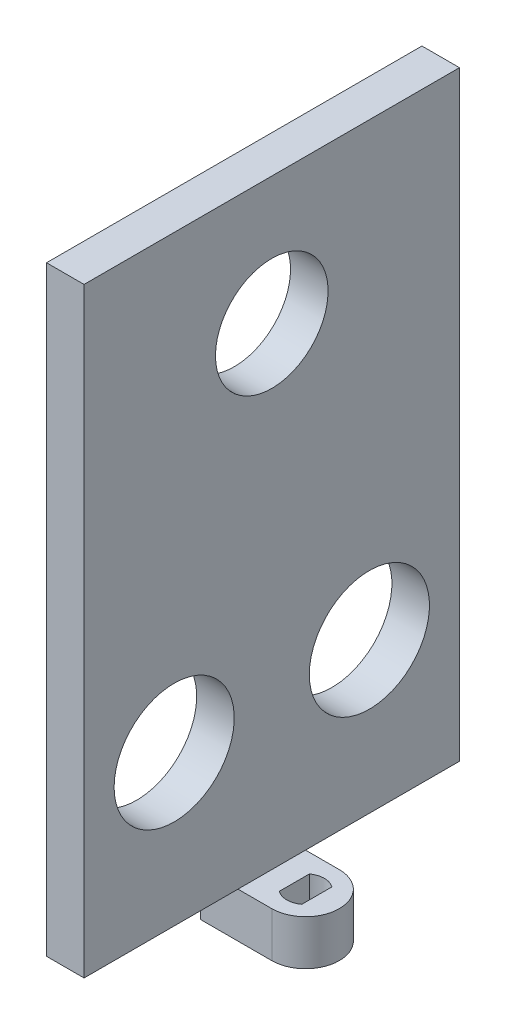
SolidWorks part; units mm, degrees
ref_plane "Alzado" through (0, 0, 0) normal (0, 0, 1) x (1, 0, 0)
ref_plane "Planta" through (0, 0, 0) normal (0, 1, 0) x (1, 0, 0)
ref_plane "Vista lateral" through (0, 0, 0) normal (1, 0, 0) x (0, 0, -1)
sketch "Croquis1" plane through (0, 0, 0) normal (0, 1, 0) x (1, 0, 0)
  line L0 (-9.5, 0) -> (-4.5, 0)
  line L1 (0, 4.5) -> (-9.5, 4.5)
  line L2 (0, 4.5) -> (0, -4.5)
  line L3 (0, -4.5) -> (-9.5, -4.5)
  line L4 (-9.5, 4.5) -> (-9.5, -4.5)
  line L5 (-1.5, -3.4467) -> (1.5, -3.4467)
  line L6 (-1.5, -3.4467) -> (-1.5, 3.4467)
  line L7 (-1.5, 3.4467) -> (1.5, 3.4467)
  line L8 (1.5, -3.4467) -> (1.5, 3.4467)
  line L9 (-1.5, -3.4467) -> (1.5, 3.4467) construction
  line L10 (-1.5, 3.4467) -> (1.5, -3.4467) construction
  line L11 (-4.5, 0) -> (4.5, 0)
  circle A0 centre (0, 0) radius 4.5
  circle A1 centre (0, 0) radius 2.5
  dimension "D1" = 9
  dimension "D2" = 5
  dimension "D3" = 3
  dimension "D4" = 5
extrude "Saliente-Extruir1" add sketch "Croquis1" along normal blind 6 contours A0 L1 L4 L0 | A0 L0 L4 L3 | A1 L6 L7 L2 A0 L11 | A1 L11 A0 L2 L5 L6 | L11 A1 L6 | L6 A1 L11 | A1 L2 L7 L6 | A1 L8 L7 L2 | A1 L6 L5 L2 | A1 L2 L5 L8 | L8 A1 L11 | L11 A1 L8 | A1 L11 A0 L2 L7 L8 | A1 L8 L5 L2 A0 L11
sketch "Croquis4" plane through (0, 6, 0) normal (0, 1, 0) x (1, 0, 0)
  line L0 (0, -4.5) -> (-9.5, -4.5) construction
  line L1 (-9.5, -25) -> (-4.5, -25)
  line L2 (-9.5, -25) -> (-9.5, 25)
  line L3 (-9.5, 25) -> (-4.5, 25)
  line L4 (-4.5, -25) -> (-4.5, 25)
  dimension "D1" = 50
  dimension "D2" = 20.5
  dimension "D3" = 5
extrude "Saliente-Extruir4" add sketch "Croquis4" along normal blind 80
sketch "Croquis5" plane through (-9.5, 0, 0) normal (-1, 0, 0) x (0, 0, 1)
  line L0 (-25, 86) -> (-25, 6) construction
  line L1 (-25, 36) -> (25, 36)
  line L2 (-25, 36) -> (-25, 16)
  line L3 (-25, 16) -> (25, 16)
  line L4 (25, 36) -> (25, 16)
  line L5 (25, 86) -> (25, 6) construction
  line L6 (-13, 26) -> (13, 26)
  line L7 (-13, 26) -> (-25, 26)
  line L8 (0, 26) -> (0, 6)
  line L9 (4.5, 6) -> (-4.5, 6) construction
  line L10 (-25, 6) -> (-4.5, 6) construction
  line L11 (25, 26) -> (-25.8331, 26)
  line L12 (0, 76.5) -> (0, 81)
  line L13 (17.5, 81) -> (-17.5, 81)
  line L14 (17.5, 81) -> (17.5, 46)
  line L15 (17.5, 46) -> (-17.5, 46)
  line L16 (-17.5, 81) -> (-17.5, 46)
  line L18 (0, 36) -> (0, 46)
  circle A0 centre (-13, 26) radius 8
  circle A1 centre (13, 26) radius 8
  circle A2 centre (0, 69) radius 7.5
  dimension "D1" = 16
  dimension "D2" = 16
  dimension "D8" = 15
  dimension "D3" = 20
  dimension "D4" = 26
  dimension "D5" = 20
  dimension "D6" = 35
  dimension "D7" = 35
  dimension "D9" = 10
  dimension "D10" = 12
  dimension "D11" = 4.5
extrude "Cortar-Extruir1" cut sketch "Croquis5" against normal blind 80
